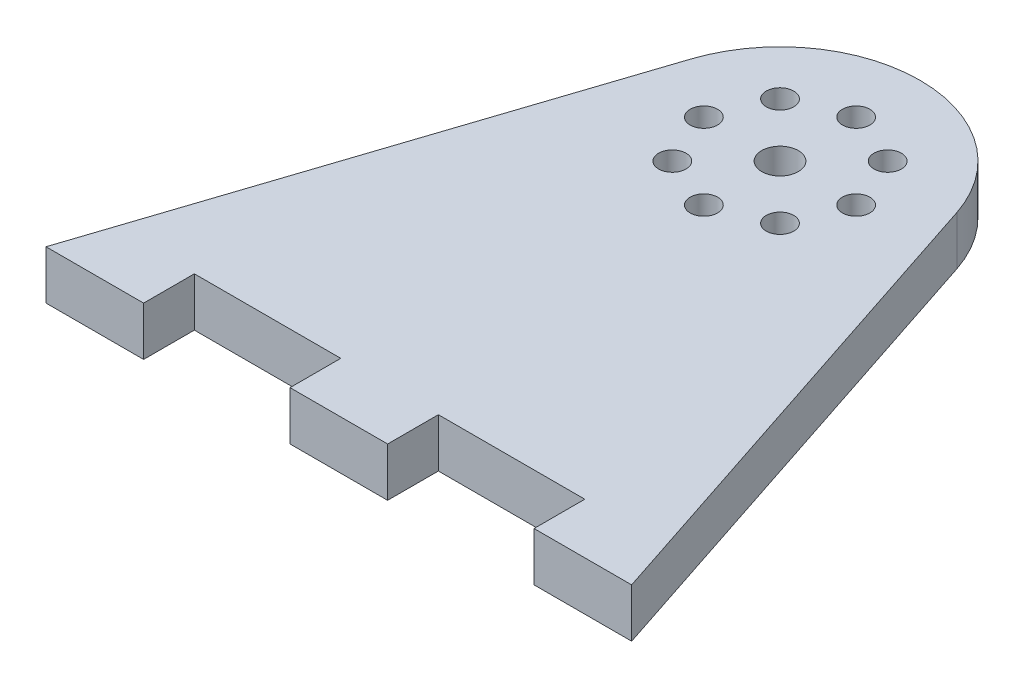
SolidWorks part; units mm, degrees
ref_plane "Front Plane" through (0, 0, 0) normal (0, 0, 1) x (1, 0, 0)
ref_plane "Top Plane" through (0, 0, 0) normal (0, 1, 0) x (1, 0, 0)
ref_plane "Right Plane" through (0, 0, 0) normal (1, 0, 0) x (0, 0, -1)
sketch "Sketch1" plane through (0, 0, 0) normal (0, 1, 0) x (1, 0, 0)
  line L0 (0, 0) -> (0, -57.404) construction
  line L1 (-38.1, -57.404) -> (-25.4, -57.404)
  line L2 (0, 0) -> (-38.1, -57.404) construction
  line L3 (0, 0) -> (38.1, -57.404) construction
  line L4 (-46.9823, 0) -> (46.9823, 0) construction
  line L5 (-38.1, -57.404) -> (-17.3029, 5.7023)
  line L6 (38.1, -57.404) -> (17.3029, 5.7023)
  line L7 (34.961, -50.8) -> (-34.961, -50.8) construction
  line L8 (6.35, -50.8) -> (6.35, -57.404)
  line L9 (-25.4, -50.8) -> (-6.35, -50.8)
  line L10 (-25.4, -50.8) -> (-25.4, -57.404)
  line L12 (-6.35, -50.8) -> (-6.35, -57.404)
  line L14 (25.4, -50.8) -> (25.4, -57.404)
  line L15 (25.4, -50.8) -> (6.35, -50.8)
  line L16 (25.4, -57.404) -> (38.1, -57.404)
  line L17 (-6.35, -57.404) -> (6.35, -57.404)
  circle A0 centre (0, 0) radius 2.3813
  circle A1 centre (-9.906, 0) radius 1.7859
  circle A2 centre (-7.0046, 7.0046) radius 1.7859
  circle A3 centre (0, 9.906) radius 1.7859
  circle A4 centre (7.0046, 7.0046) radius 1.7859
  circle A5 centre (9.906, 0) radius 1.7859
  circle A6 centre (7.0046, -7.0046) radius 1.7859
  circle A7 centre (0, -9.906) radius 1.7859
  circle A8 centre (-7.0046, -7.0046) radius 1.7859
  circle A9 centre (0, 0) radius 18.2183 construction
  arc A10 (-17.3029, 5.7023) -> (17.3029, 5.7023) centre (0, 0) cw
  point P3 (0, 0)
  point P7 (0, -57.404)
  point P11 (0, 0)
  point P29 (0, 0)
  point P34 (0, -50.8)
  dimension "D3" = 4.7625
  dimension "D4" = 3.5719
  dimension "D7" = 6.604
  dimension "D1" = 57.404
  dimension "D2" = 76.2
  dimension "D5" = 9.906
  dimension "D9" = 6.35
  dimension "D10" = 19.05
  dimension "D6" = 8
extrude "Boss-Extrude1" add sketch "Sketch1" along normal blind 6.35
fillet "Fillet1" [suppressed] radius 3.175
